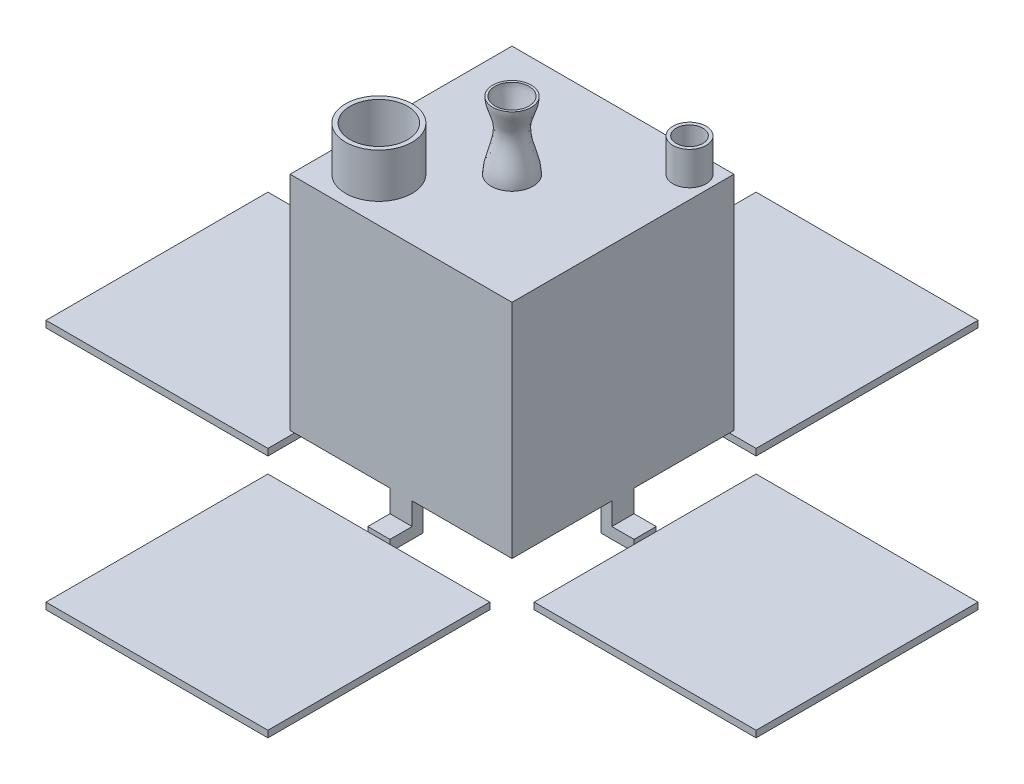
SolidWorks part; units mm, degrees
other "Камера2"
other "Камера4"
ref_plane "Спереди" through (0, 0, 0) normal (0, 0, 1) x (1, 0, 0)
ref_plane "Сверху" through (0, 0, 0) normal (0, 1, 0) x (1, 0, 0)
ref_plane "Справа" through (0, 0, 0) normal (1, 0, 0) x (0, 0, -1)
sketch "Эскиз1" plane through (0, 0, 0) normal (0, 1, 0) x (1, 0, 0)
  line L0 (0, 50) -> (0, -50) construction
  line L1 (-50, 50) -> (50, 50)
  line L2 (-50, 50) -> (-50, -50)
  line L3 (-50, -50) -> (50, -50)
  line L4 (50, 50) -> (50, -50)
  line L5 (-50, 0) -> (50, 0) construction
  dimension "D1" = 100
extrude "Бобышка-Вытянуть1" add sketch "Эскиз1" along normal blind 100
sketch "Эскиз2" plane through (0, 0, 0) normal (0, -1, 0) x (1, 0, 0)
  line L0 (-50, -50) -> (-50, 50) construction
  line L1 (-50, 50) -> (50, -50) construction
  line L2 (-45, 45) -> (-45, -45)
  line L3 (-45, -45) -> (45, -45)
  line L4 (45, 45) -> (45, -45)
  line L5 (50, -50) -> (-50, -50) construction
  line L6 (-45, 45) -> (45, 45)
  dimension "D1" = 5
  dimension "D2" = 5
extrude "Вырез-Вытянуть1" [suppressed] cut sketch "Эскиз2" against normal blind 95
ref_plane "Midle" through (0, 0, 0) normal (0, 0, 1) x (1, 0, 0)
sketch "Эскиз3" plane through (0, 0, 0) normal (0, 0, 1) x (1, 0, 0)
  line L8 (50, 50) -> (-6.7995, 50) construction
  line L9 (50, 100) -> (50, 0) construction
  line L10 (45, -15) -> (50, -10) construction
  line L11 (60, -10) -> (60, -15)
  line L12 (60, -10) -> (50, -10)
  line L13 (60, -15) -> (45, -15)
  line L14 (45, 0) -> (45, -15)
  line L15 (50, 0) -> (50, -10)
  line L16 (50, 0) -> (45, 0)
extrude "Бобышка-Вытянуть2" add sketch "Эскиз3" along normal blind 5 and the other way blind 5
sketch "Эскиз4" plane through (0, -15, 0) normal (0, -1, 0) x (1, 0, 0)
  line L0 (60, 0) -> (160, 0) construction
  line L1 (60, -5) -> (60, 5) construction
  line L2 (60, -50) -> (60, 50)
  line L3 (60, 50) -> (160, 50)
  line L4 (160, 50) -> (160, -50)
  line L5 (60, -50) -> (160, -50)
extrude "Бобышка-Вытянуть3" add sketch "Эскиз4" against normal blind 3
sketch "Эскиз5" plane through (0, 0, 0) normal (0, 0, 1) x (1, 0, 0)
  line L0 (0, 0) -> (0, 100) construction
  line L1 (-50, 100) -> (50, 100) construction
pattern_circular "Круговой массив1" count 4 every 90 about axis through (0, 0, 0) along (0, 1, 0) of "Бобышка-Вытянуть3", "Бобышка-Вытянуть2"
sketch "Эскиз6" plane through (0, 100, 0) normal (0, 1, 0) x (1, 0, 0)
  circle A0 centre (0, 0) radius 10
extrude "Бобышка-Вытянуть4" [suppressed] add sketch "Эскиз6" along normal blind 15
chamfer "Фаска1" [suppressed] distance 3 angle 45
sketch "Эскиз7" plane through (0, 100, 0) normal (0, 1, 0) x (1, 0, 0)
  line L0 (-50, -50) -> (50, -50) construction
  line L1 (-50, 50) -> (-50, -50) construction
  circle A0 centre (-30, -30) radius 15
  circle A1 centre (-30, -30) radius 13
  dimension "D1" = 20
  dimension "D2" = 20
extrude "Бобышка-Вытянуть5" add sketch "Эскиз7" along normal blind 20
sketch "Эскиз8" plane through (0, 100, 0) normal (0, 1, 0) x (1, 0, 0)
  line L0 (50, -50) -> (50, 50) construction
  line L1 (50, 50) -> (-50, 50) construction
  circle A0 centre (40, 40) radius 7.5
  circle A1 centre (40, 40) radius 6
  dimension "D1" = 10
  dimension "D2" = 10
  dimension "D3" = 15
extrude "Бобышка-Вытянуть6" add sketch "Эскиз8" along normal blind 15
sketch "Эскиз10" plane through (0, 0, 0) normal (0, 0, 1) x (1, 0, 0)
  line L0 (0, 100) -> (0, 130) construction
  line L1 (-50, 100) -> (50, 100) construction
  line L2 (8.6806, 130.4458) -> (7.6806, 130.4458)
  line L3 (9.4365, 100) -> (8.4365, 100)
  spline S0 degree 3 poles (7.6806, 130.4458) (7.6806, 127.0362) (1.6694, 117.3031) (8.4365, 106.7175) (8.4365, 100) knots 0 0 0 0 0.331036 1 1 1 1
  spline S1 degree 1 poles (8.6806, 130.4458) (9.4365, 100) knots 0 0 1 1 construction
  spline S2 degree 3 poles (8.6806, 130.4458) (8.6806, 129.743) (8.5226, 128.323) (7.9902, 126.3414) (7.3224, 124.4354) (6.6636, 122.6001) (6.1439, 120.8287) (5.8105, 118.5381) (6.0082, 115.5365) (6.893, 111.7864) (8.4428, 106.6438) (9.4365, 102.6801) (9.4365, 100) knots 0 0 0 0 0.0625 0.125 0.1875 0.25 0.3125 0.375 0.5 0.625 0.75 1 1 1 1
  dimension "D1" = 30
  dimension "D2" = 1
revolve "Повернуть1" add sketch "Эскиз10" angle 360 about L0
sketch "Эскиз11" plane through (0, 0, 0) normal (0, -1, 0) x (1, 0, 0)
  circle A0 centre (-26.9274, 25.6159) radius 7.21
extrude "Вырез-Вытянуть2" cut sketch "Эскиз11" against normal blind 5
sketch "Эскиз13" plane through (0, 0, 0) normal (0, 0, 1) x (1, 0, 0)
  point P5 (0, 50)
ref_point "."
equation "\"D1\"=10"
